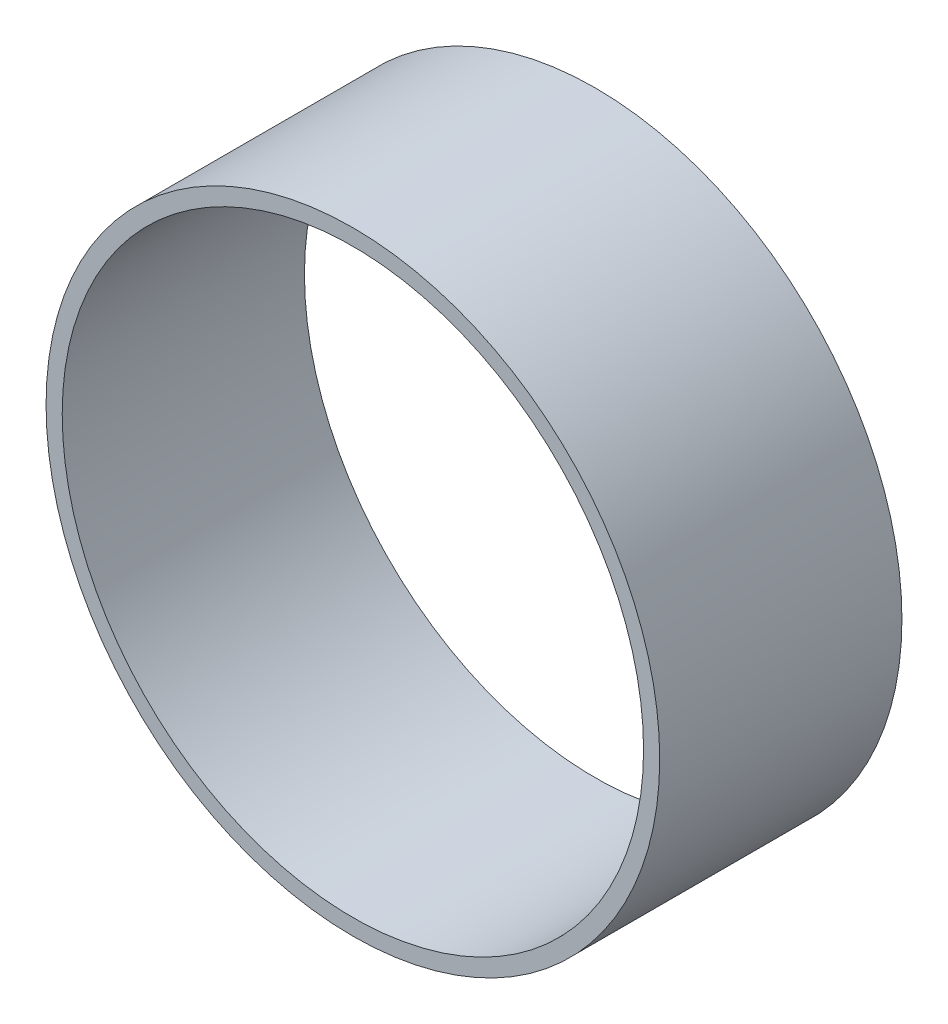
SolidWorks part; units mm, degrees
material "6061 Alloy"
ref_plane "Front Plane" through (0, 0, 0) normal (0, 0, 1) x (1, 0, 0)
ref_plane "Top Plane" through (0, 0, 0) normal (0, 1, 0) x (1, 0, 0)
ref_plane "Right Plane" through (0, 0, 0) normal (1, 0, 0) x (0, 0, -1)
sketch "Sketch1" plane through (0, 0, 0) normal (0, 0, 1) x (1, 0, 0)
  circle A0 centre (0, 0) radius 190
  circle A1 centre (0, 0) radius 180
  dimension "D1" = 380
  dimension "D2" = 10
extrude "Boss-Extrude1" add sketch "Sketch1" along normal blind 150
